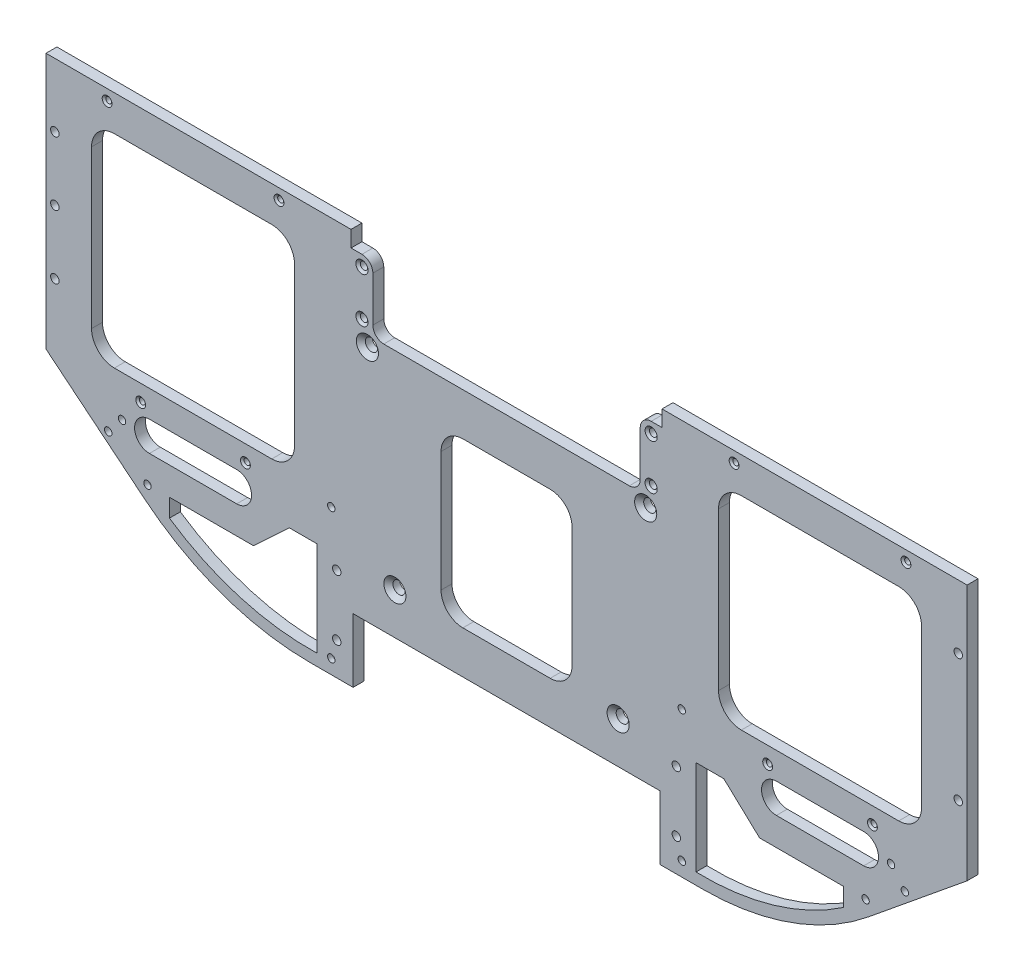
SolidWorks part; units mm, degrees
material "Acrylic (Medium-high impact)"
ref_plane "Front Plane" through (0, 0, 0) normal (0, 0, 1) x (1, 0, 0)
ref_plane "Top Plane" through (0, 0, 0) normal (0, 1, 0) x (1, 0, 0)
ref_plane "Right Plane" through (0, 0, 0) normal (1, 0, 0) x (0, 0, -1)
sketch "Sketch1" plane through (0, 0, 0) normal (0, 0, 1) x (1, 0, 0)
  line L0 (-85.5662, -233.3625) -> (-68.1037, -233.3625) construction
  line L1 (131.2863, 23.8125) -> (131.2863, -87.3125) construction
  line L2 (85.5663, 23.8125) -> (131.2863, 23.8125) construction
  line L3 (85.5663, -144.4625) -> (85.5663, 23.8125) construction
  line L6 (-79.2163, -3.175) -> (79.2162, -3.175) construction
  line L7 (-296.7037, -233.3625) -> (-68.1037, -233.3625)
  line L8 (131.2863, 23.8125) -> (131.2863, -87.3125)
  line L9 (85.5663, 23.8125) -> (131.2863, 23.8125)
  line L10 (85.5663, -3.175) -> (85.5663, 23.8125)
  line L11 (-131.6037, 20.5105) -> (-233.2037, 20.5105)
  line L12 (-131.6037, -3.175) -> (-131.6037, 20.5105)
  line L13 (-131.6037, -3.175) -> (85.5663, -3.175)
  line L14 (95.0913, -144.4625) -> (28.2786, -199.0142)
  line L15 (-182.4037, -196.215) -> (-182.4037, -51.435) construction
  line L16 (-93.5037, -196.215) -> (-271.3037, -196.215) construction
  line L17 (-268.1287, -51.435) -> (-96.6787, -51.435) construction
  line L18 (-459.8987, -144.4625) -> (-393.0861, -199.0142)
  line L19 (-233.2037, -3.175) -> (-450.3737, -3.175)
  line L20 (-233.2037, -3.175) -> (-233.2037, 20.5105)
  line L21 (-450.3737, -3.175) -> (-450.3737, -20.955)
  line L22 (-450.3737, -20.955) -> (-496.0937, -20.955)
  line L23 (-496.0937, -20.955) -> (-496.0937, -87.3125)
  line L24 (-496.0937, -20.955) -> (-450.3737, -20.955) construction
  line L25 (-450.3737, -20.955) -> (-450.3737, -144.4625) construction
  line L26 (-496.0937, -87.3125) -> (-496.0937, -20.955) construction
  arc A0 (-68.1037, -233.3625) -> (28.2786, -199.0142) centre (-68.1037, -80.9625) ccw construction
  arc A1 (95.0913, -144.4625) -> (131.2863, -87.3125) centre (-12.3507, -36.3792) ccw construction
  arc A2 (-68.1037, -233.3625) -> (28.2786, -199.0142) centre (-68.1037, -80.9625) ccw
  arc A3 (95.0913, -144.4625) -> (131.2863, -87.3125) centre (-12.3507, -36.3792) ccw
  arc A4 (-459.8987, -144.4625) -> (-496.0937, -87.3125) centre (-352.4568, -36.3792) cw
  arc A5 (-296.7037, -233.3625) -> (-393.0861, -199.0142) centre (-296.7037, -80.9625) cw
  point P39 (-182.4037, 20.5105)
  point P41 (-182.4037, -233.3625)
extrude "Boss-Extrude1" add sketch "Sketch1" along normal blind 6.35
sketch "Sketch2" plane through (0, 0, 6.35) normal (0, 0, 1) x (1, 0, 0)
  line L0 (-339.4075, -166.116) -> (-390.2075, -166.116) construction
  line L4 (-423.8625, -37.0786) -> (-423.8625, -128.6564)
  line L5 (-319.0186, -23.8125) -> (-410.5964, -23.8125)
  line L6 (-305.7525, -128.6564) -> (-305.7525, -37.0786)
  line L7 (-410.5964, -141.9225) -> (-319.0186, -141.9225)
  line L8 (-423.8625, -37.0786) -> (-423.8625, -128.6564)
  line L9 (-319.0186, -23.8125) -> (-410.5964, -23.8125)
  line L10 (-305.7525, -128.6564) -> (-305.7525, -37.0786)
  line L11 (-410.5964, -141.9225) -> (-319.0186, -141.9225)
  line L13 (-292.6397, -178.6479) -> (-292.6397, -214.3) construction
  line L14 (-292.6397, -171.5333) -> (-292.6397, -226.6383)
  line L15 (-326.4504, -188.0036) -> (-308.8, -171.5333) construction
  line L16 (-365.5822, -190.9762) -> (-335.4294, -190.9762) construction
  line L17 (-329.6361, -190.9762) -> (-308.8, -171.5333)
  line L18 (-378.5543, -190.9762) -> (-329.6361, -190.9762)
  line L19 (-308.8, -171.5333) -> (-292.6397, -171.5333)
  line L20 (-378.5543, -201.538) -> (-378.5543, -190.9762)
  line L21 (-339.4075, -174.752) -> (-390.2075, -174.752)
  line L24 (-339.4075, -157.48) -> (-390.2075, -157.48)
  line L25 (-182.4037, 20.5105) -> (-182.4037, -233.3625) construction
  line L26 (-131.6037, 20.5105) -> (-233.2037, 20.5105) construction
  line L29 (-296.7037, -233.3625) -> (-68.1037, -233.3625) construction
  line L30 (-25.4, -166.116) -> (25.4, -166.116) construction
  line L31 (-25.4, -174.752) -> (25.4, -174.752)
  line L32 (-25.4, -157.48) -> (25.4, -157.48)
  line L33 (13.7468, -201.538) -> (13.7468, -190.9762)
  line L34 (-56.0075, -171.5333) -> (-72.1678, -171.5333)
  line L35 (13.7468, -190.9762) -> (-35.1714, -190.9762)
  line L36 (-35.1714, -190.9762) -> (-56.0075, -171.5333)
  line L37 (-72.1678, -171.5333) -> (-72.1678, -226.6383)
  line L38 (45.7889, -141.9225) -> (-45.7889, -141.9225)
  line L39 (-59.055, -128.6564) -> (-59.055, -37.0786)
  line L40 (-45.7889, -23.8125) -> (45.7889, -23.8125)
  line L41 (59.055, -37.0786) -> (59.055, -128.6564)
  arc A4 (-423.8625, -128.6564) -> (-410.5964, -141.9225) centre (-410.5964, -128.6564) ccw
  arc A5 (-410.5964, -23.8125) -> (-423.8625, -37.0786) centre (-410.5964, -37.0786) ccw
  arc A6 (-305.7525, -37.0786) -> (-319.0186, -23.8125) centre (-319.0186, -37.0786) ccw
  arc A7 (-319.0186, -141.9225) -> (-305.7525, -128.6564) centre (-319.0186, -128.6564) ccw
  arc A8 (-423.8625, -128.6564) -> (-410.5964, -141.9225) centre (-410.5964, -128.6564) ccw
  arc A9 (-410.5964, -23.8125) -> (-423.8625, -37.0786) centre (-410.5964, -37.0786) ccw
  arc A10 (-305.7525, -37.0786) -> (-319.0186, -23.8125) centre (-319.0186, -37.0786) ccw
  arc A11 (-319.0186, -141.9225) -> (-305.7525, -128.6564) centre (-319.0186, -128.6564) ccw
  arc A13 (-339.4075, -174.752) -> (-339.4075, -157.48) centre (-339.4075, -166.116) ccw
  arc A15 (-377.1442, -202.4833) -> (-336.1163, -221.2644) centre (-296.7037, -80.9625) ccw construction
  arc A17 (-378.5543, -201.538) -> (-292.6397, -226.6383) centre (-296.7037, -80.9625) ccw
  arc A19 (-390.2075, -157.48) -> (-390.2075, -174.752) centre (-390.2075, -166.116) ccw
  arc A20 (-25.4, -174.752) -> (-25.4, -157.48) centre (-25.4, -166.116) cw
  arc A21 (25.4, -157.48) -> (25.4, -174.752) centre (25.4, -166.116) cw
  arc A22 (13.7468, -201.538) -> (-72.1678, -226.6383) centre (-68.1038, -80.9625) cw
  arc A23 (-45.7889, -141.9225) -> (-59.055, -128.6564) centre (-45.7889, -128.6564) cw
  arc A24 (-59.055, -37.0786) -> (-45.7889, -23.8125) centre (-45.7889, -37.0786) cw
  arc A25 (45.7889, -23.8125) -> (59.055, -37.0786) centre (45.7889, -37.0786) cw
  arc A26 (59.055, -128.6564) -> (45.7889, -141.9225) centre (45.7889, -128.6564) cw
  point P10 (-364.8075, -166.116)
  point P27 (0, -166.116)
  dimension "D2" = 8.636
  dimension "D3" = 50.8
  dimension "D1" = 0
extrude "Cut-Extrude1" cut sketch "Sketch2" against normal through all
hole_wizard "CSK for 1/4 Flat Head Machine Screw (100)1" positions "Sketch3" profile "Sketch4" countersink size "1/4" standard "ANSI Inch" end condition up to next
sketch "Sketch3" plane through (0, 0, 6.35) normal (0, 0, 1) x (1, 0, 0)
  point P0 (-247.3642, -172.085)
  point P3 (-263.3662, -57.785)
  point P6 (-117.4432, -172.085)
  point P9 (-101.4412, -57.785)
sketch "Sketch4" plane through (-247.3642, -172.085, 6.35) normal (1, 0, 0) x (0, -1, 0)
  line L0 (0, 0) -> (0, 6.35)
  line L1 (0, 6.35) -> (3.5712, 6.35)
  line L2 (3.5712, 6.35) -> (3.5712, 2.4063)
  line L3 (3.5712, 2.4063) -> (6.4389, 0)
  line L5 (6.4389, 0) -> (0, 0)
  line L6 (-3.5712, 2.4063) -> (-6.4389, 0) construction
  line L11 (0, -6.35) -> (0, 107.95) construction
  dimension "Thru Hole Dia." = 7.1425
  dimension "Thru Hole Depth" = 6.35
  dimension "Near C'Sink Dia." = 12.8778
  dimension "Near C'Sink Angle" = 100
hole_wizard "CSK for #4 Flat Head Machine Screw (100)1" positions "Sketch5" profile "Sketch6" countersink size "#4" standard "ANSI Inch" end condition through all
sketch "Sketch5" plane through (0, 0, 6.35) normal (0, 0, 1) x (1, 0, 0)
  point P0 (-334.3275, -151.5305)
  point P3 (-395.2875, -151.5305)
  point P6 (-314.8013, -9.525)
  point P9 (-414.8137, -9.525)
  point P12 (30.48, -151.5305)
  point P15 (-30.48, -151.5305)
  point P18 (50.0062, -9.525)
  point P21 (-50.0062, -9.525)
sketch "Sketch6" plane through (-334.3275, -151.5305, 6.35) normal (1, 0, 0) x (0, -1, 0)
  line L0 (0, 0) -> (0, 6.35)
  line L1 (0, 6.35) -> (1.7272, 6.35)
  line L2 (1.7272, 6.35) -> (1.7272, 0.9484)
  line L3 (1.7272, 0.9484) -> (2.8575, 0)
  line L5 (2.8575, 0) -> (0, 0)
  line L6 (-1.7272, 0.9484) -> (-2.8575, 0) construction
  line L11 (0, -6.35) -> (0, 107.95) construction
  dimension "Thru Hole Dia." = 3.4544
  dimension "Thru Hole Depth" = 6.35
  dimension "Near C'Sink Dia." = 5.715
  dimension "Near C'Sink Angle" = 100
sketch "Sketch7" plane through (0, 0, 6.35) normal (0, 0, 1) x (1, 0, 0)
  line L0 (-271.672, -233.3625) -> (-271.672, -196.215)
  line L1 (-271.672, -196.215) -> (-93.1354, -196.215)
  line L2 (-182.4037, -196.215) -> (-182.4037, -233.3625) construction
  line L3 (-296.7037, -233.3625) -> (-68.1037, -233.3625) construction
  line L4 (-93.5037, -196.215) -> (-271.3037, -196.215) construction
  line L5 (-93.1354, -233.3625) -> (-271.672, -233.3625)
  line L6 (-93.1354, -233.3625) -> (-93.1354, -196.215)
extrude "Cut-Extrude2" cut sketch "Sketch7" against normal up to next
hole_wizard "#6 Clearance Hole1" positions "Sketch21" profile "Sketch31" hole size "#6" standard "ANSI Inch" end condition up to next
sketch "Sketch21" plane through (-452.3171, -175.5643, 0) normal (0, 0, -1) x (-1, 0, 0)
  point P0 (-60.9984, -15.4755)
  point P3 (-167.9324, -49.5432)
  point P6 (-167.9324, 26.727)
  point P9 (-371.8944, 26.727)
  point P12 (-371.8944, -49.5432)
  point P15 (-478.8284, -15.4755)
sketch "Sketch31" plane through (-391.3187, -191.0397, 0) normal (1, 0, 0) x (0, 1, 0)
  line L0 (0, 0) -> (0, 6.35)
  line L1 (0, 6.35) -> (2.1526, 6.35)
  line L2 (2.1526, 6.35) -> (2.1526, 0)
  line L5 (2.1526, 0) -> (0, 0)
  line L11 (0, -6.35) -> (0, 107.95) construction
  dimension "Thru Hole Dia." = 4.3053
  dimension "Thru Hole Depth" = 6.35
hole_wizard "#6 Plastic Insert" positions "Sketch41" profile "Sketch51" legacy
sketch "Sketch41" plane through (-452.3171, -175.5643, 0) normal (0, 0, -1) x (-1, 0, 0)
  point P0 (-60.9984, -15.4755)
  point P3 (-167.9324, -49.5432)
  point P6 (-167.9324, 26.727)
  point P9 (-371.8944, 26.727)
  point P12 (-371.8944, -49.5432)
  point P15 (-478.8284, -15.4755)
sketch "Sketch51" plane through (-391.3187, -191.0397, 0) normal (1, 0, 0) x (0, 1, 0)
  line L0 (0, 0) -> (0, 3.81)
  line L1 (0, 3.81) -> (2.5273, 3.81)
  line L2 (2.5273, 3.81) -> (2.6543, 0)
  line L3 (2.6543, 0) -> (0, 0)
  line L4 (0, 110) -> (0, -10) construction
  dimension "Minor Diameter" = 5.0546
  dimension "Depth" = 3.81
  dimension "Major Diameter" = 5.3086
other "#6 Plastic Insert Hole<1>"
hole_wizard "#6 Clearance Hole2" positions "Sketch52" profile "Sketch53" hole size "#6" standard "ANSI Inch" end condition through all
sketch "Sketch52" plane through (0, 0, 0) normal (0, 0, -1) x (-1, 0, 0)
  point P0 (459.5177, -126.1745)
  point P3 (479.9012, -91.8845)
  point P6 (486.5052, -36.449)
  point P9 (-94.7103, -126.1745)
  point P12 (-121.9518, -83.6295)
  point P15 (-98.2663, 15.875)
sketch "Sketch53" plane through (-459.5177, -126.1745, 0) normal (1, 0, 0) x (0, 1, 0)
  line L0 (0, 0) -> (0, 6.35)
  line L1 (0, 6.35) -> (2.1526, 6.35)
  line L2 (2.1526, 6.35) -> (2.1526, 0)
  line L5 (2.1526, 0) -> (0, 0)
  line L11 (0, -6.35) -> (0, 107.95) construction
  dimension "Thru Hole Dia." = 4.3053
  dimension "Thru Hole Depth" = 6.35
sketch "Sketch54" plane through (0, 0, 6.35) normal (0, 0, 1) x (1, 0, 0)
  line L0 (-91.9162, -51.435) -> (-272.8912, -51.435) construction
  line L1 (-93.5037, -49.8475) -> (-271.3037, -49.8475) construction
  line L2 (-93.5037, -49.8475) -> (-93.5037, 20.5105) construction
  line L3 (-93.5037, 20.5105) -> (-271.3037, 20.5105) construction
  line L4 (-271.3037, -49.8475) -> (-271.3037, 20.5105) construction
  line L7 (-131.6037, 20.5105) -> (-233.2037, 20.5105) construction
  line L8 (-272.8912, -38.735) -> (-260.1912, -38.735)
  line L9 (-260.1912, -51.435) -> (-260.1912, -38.735)
  line L10 (-104.6162, -51.435) -> (-260.1912, -51.435)
  line L11 (-272.8912, -38.735) -> (-272.8912, 22.098)
  line L12 (-91.9162, 22.098) -> (-272.8912, 22.098)
  line L13 (-91.9162, -38.735) -> (-91.9162, 22.098)
  line L14 (-272.8912, -51.435) -> (-272.8912, 22.098) construction
  line L17 (-91.9162, -38.735) -> (-104.6162, -38.735)
  line L18 (-104.6162, -51.435) -> (-104.6162, -38.735)
  line L19 (-91.9162, -51.435) -> (-91.9162, 22.098) construction
  dimension "D1" = 1.5875
  dimension "D2" = 12.7
  dimension "D3" = 12.7
  dimension "D4" = 12.7
  dimension "D5" = 12.7
extrude "Cut-Extrude3" cut sketch "Sketch54" against normal up to next
sketch "Sketch55" plane through (0, 0, 6.35) normal (0, 0, 1) x (1, 0, 0)
  line L0 (-91.9162, -38.735) -> (-91.9162, -3.175) construction
  line L1 (-91.9162, -12.572) -> (-104.6162, -12.572)
  line L2 (-91.9162, -12.572) -> (-91.9162, -38.735)
  line L3 (-91.9162, -38.735) -> (-104.6162, -38.735)
  line L4 (-104.6162, -12.572) -> (-104.6162, -38.735)
  line L6 (-182.4037, -51.435) -> (-182.4037, -196.215) construction
  line L7 (-260.1912, -51.435) -> (-104.6162, -51.435) construction
  line L8 (-93.1354, -196.215) -> (-271.672, -196.215) construction
  line L9 (-260.1912, -12.572) -> (-260.1912, -38.735)
  line L10 (-272.8912, -38.735) -> (-260.1912, -38.735)
  line L11 (-272.8912, -12.572) -> (-272.8912, -38.735)
  line L12 (-272.8912, -12.572) -> (-260.1912, -12.572)
  line L13 (-93.5037, -9.397) -> (-134.7787, -9.397) construction
  dimension "D1" = 12.7
  dimension "D2" = 3.175
extrude "Boss-Extrude2" add sketch "Sketch55" against normal through all
fillet "Fillet3" radius 6.35 4 edges at (-104.6162, -12.572, 3.175) (-104.6162, -51.435, 3.175) (-260.1912, -51.435, 3.175) (-260.1912, -12.572, 3.175)
hole_wizard "CSK for #6 Flat Head Machine Screw (100)1" positions "Sketch56" profile "Sketch57" countersink size "#6" standard "ANSI Inch" end condition through all
sketch "Sketch56" plane through (0, 0, 6.35) normal (0, 0, 1) x (1, 0, 0)
  line L0 (-110.5963, -40.514) -> (-110.5963, -49.8475) construction
  line L2 (-95.0912, -49.8475) -> (-161.4487, -49.8475) construction
  line L3 (-101.4412, -40.514) -> (-116.6812, -40.514) construction
  line L4 (-110.5963, -45.1807) -> (-98.2662, -45.1807) construction
  point P0 (-266.5412, -18.922)
  point P8 (-98.2662, -18.922)
  point P31 (-98.2662, -45.1807)
  point P32 (-266.5412, -45.1807)
sketch "Sketch57" plane through (-266.5412, -18.922, 6.35) normal (1, 0, 0) x (0, -1, 0)
  line L0 (0, 0) -> (0, 6.35)
  line L1 (0, 6.35) -> (2.1526, 6.35)
  line L2 (2.1526, 6.35) -> (2.1526, 1.1669)
  line L3 (2.1526, 1.1669) -> (3.5433, 0)
  line L5 (3.5433, 0) -> (0, 0)
  line L6 (-2.1526, 1.1669) -> (-3.5433, 0) construction
  line L11 (0, -6.35) -> (0, 107.95) construction
  dimension "Thru Hole Dia." = 4.3053
  dimension "Thru Hole Depth" = 6.35
  dimension "Near C'Sink Dia." = 7.0866
  dimension "Near C'Sink Angle" = 100
sketch "Sketch58" plane through (0, 0, 6.35) normal (0, 0, 1) x (1, 0, 0)
  line L1 (-201.4537, -123.825) -> (-163.3537, -123.825) construction
  line L2 (-144.3037, -171.45) -> (-220.5037, -171.45)
  line L3 (-144.3037, -171.45) -> (-144.3037, -76.2)
  line L4 (-144.3037, -76.2) -> (-220.5037, -76.2)
  line L5 (-182.4037, -95.25) -> (-182.4037, -152.4) construction
  line L6 (-163.3537, -95.25) -> (-163.3537, -152.4) construction
  line L7 (-201.4537, -95.25) -> (-201.4537, -152.4) construction
  line L8 (-220.5037, -171.45) -> (-220.5037, -76.2)
  line L9 (-144.3037, -171.45) -> (-220.5037, -76.2) construction
  line L10 (-144.3037, -76.2) -> (-220.5037, -171.45) construction
  arc A0 (-163.3537, -95.25) -> (-201.4537, -95.25) centre (-182.4037, -95.25) ccw construction
  arc A1 (-201.4537, -152.4) -> (-163.3537, -152.4) centre (-182.4037, -152.4) ccw construction
  point P0 (-182.4037, -123.825)
  point P9 (-182.4037, -123.825)
  dimension "D1" = 57.15
  dimension "D2" = 38.1
  dimension "D3" = 76.2
extrude "Cut-Extrude4" cut sketch "Sketch58" against normal through all
sketch "Sketch60" plane through (0, 0, 6.35) normal (0, 0, 1) x (1, 0, 0)
  line L0 (85.5663, 23.8125) -> (85.5663, -152.2395)
  line L1 (28.2786, -199.0142) -> (95.0913, -144.4625) construction
  line L2 (131.2863, 23.8125) -> (85.5663, 23.8125) construction
  line L3 (131.2863, -87.3125) -> (131.2863, 23.8125) construction
  line L4 (131.2863, 23.8125) -> (85.5663, 23.8125)
  line L5 (131.2863, -87.3125) -> (131.2863, 23.8125)
  line L6 (85.5663, -152.2395) -> (95.0913, -144.4625)
  line L7 (-450.3737, -20.955) -> (-496.0937, -20.955) construction
  line L8 (-496.0937, -20.955) -> (-496.0937, -87.3125) construction
  line L9 (-459.8987, -144.4625) -> (-393.0861, -199.0142) construction
  line L10 (-450.3737, -20.955) -> (-496.0937, -20.955)
  line L11 (-496.0937, -20.955) -> (-496.0937, -87.3125)
  line L12 (-459.8987, -144.4625) -> (-450.3737, -152.2395)
  line L13 (-450.3737, -20.955) -> (-450.3737, -152.2395)
  arc A0 (95.0913, -144.4625) -> (131.2863, -87.3125) centre (-12.3507, -36.3792) ccw construction
  arc A1 (95.0913, -144.4625) -> (131.2863, -87.3125) centre (-12.3507, -36.3792) ccw
  arc A2 (-496.0937, -87.3125) -> (-459.8987, -144.4625) centre (-352.4568, -36.3792) ccw construction
  arc A3 (-496.0937, -87.3125) -> (-459.8987, -144.4625) centre (-352.4568, -36.3792) ccw
extrude "Cut-Extrude5" cut sketch "Sketch60" against normal through all
hole_wizard "CSK for #8 Flat Head Machine Screw (100)2" positions "Sketch61" profile "Sketch62" countersink size "#8" standard "ANSI Inch" end condition up to next
sketch "Sketch61" plane through (0, 0, 0) normal (0, 0, -1) x (-1, 0, 0)
  line L0 (281.197, -160.0558) -> (281.197, -233.3625) construction
  line L1 (296.7037, -233.3625) -> (271.672, -233.3625) construction
  line L5 (271.672, -186.69) -> (182.4037, -186.69) construction
  line L6 (182.4037, -186.69) -> (93.1355, -186.69) construction
  line L9 (445.2302, -3.175) -> (445.2302, -77.2147) construction
  line L10 (445.2302, -77.2147) -> (445.2302, -151.2545) construction
  line L11 (182.4037, -196.215) -> (182.4037, -51.435) construction
  line L12 (271.672, -196.215) -> (93.1354, -196.215) construction
  line L13 (110.9662, -51.435) -> (253.8412, -51.435) construction
  line L15 (-80.4228, -77.2147) -> (-80.4228, -151.2545) construction
  line L16 (-80.4228, -3.175) -> (-80.4228, -77.2147) construction
  line L17 (93.1355, -186.69) -> (182.4037, -186.69) construction
  line L18 (83.6104, -160.0558) -> (83.6104, -233.3625) construction
  point P0 (281.197, -214.3125)
  point P2 (281.197, -179.1058)
  point P36 (445.2302, -77.2147)
  point P41 (445.2302, -40.1949)
  point P45 (445.2302, -114.2346)
  point P61 (-80.4228, -114.2346)
  point P62 (-80.4228, -40.1949)
  point P64 (83.6104, -179.1058)
  point P65 (83.6104, -214.3125)
  dimension "D1" = 19.05
  dimension "D2" = 19.05
sketch "Sketch62" plane through (-281.197, -214.3125, 0) normal (1, 0, 0) x (0, 1, 0)
  line L0 (0, 0) -> (0, 6.35)
  line L1 (0, 6.35) -> (2.4574, 6.35)
  line L2 (2.4574, 6.35) -> (2.4574, 1.4759)
  line L3 (2.4574, 1.4759) -> (4.2164, 0)
  line L5 (4.2164, 0) -> (0, 0)
  line L6 (-2.4574, 1.4759) -> (-4.2164, 0) construction
  line L11 (0, -6.35) -> (0, 107.95) construction
  dimension "Thru Hole Dia." = 4.9149
  dimension "Thru Hole Depth" = 6.35
  dimension "Near C'Sink Dia." = 8.4328
  dimension "Near C'Sink Angle" = 100
fillet "Fillet4" radius 12.7 4 edges at (-144.3037, -171.45, 3.175) (-144.3037, -76.2, 3.175) (-220.5037, -76.2, 3.175) (-220.5037, -171.45, 3.175)
hole_wizard "CSK for #6 Flat Head Machine Screw (100)2" positions "Sketch63" profile "Sketch64" countersink size "#6" standard "ANSI Inch" end condition up to next
sketch "Sketch63" plane through (0, 0, 0) normal (0, 0, -1) x (-1, 0, 0)
  circle A0 centre (406.1283, -165.8215) radius 2.1527 construction
  circle A1 centre (414.1604, -175.659) radius 2.1526 construction
  circle A2 centre (-41.3183, -165.8233) radius 2.1527 construction
  circle A3 centre (-49.3504, -175.6607) radius 2.1526 construction
  point P0 (414.1604, -175.659)
  point P2 (406.1283, -165.8215)
  point P10 (-41.3183, -165.8233)
  point P12 (-49.3504, -175.6607)
sketch "Sketch64" plane through (-414.1604, -175.659, 0) normal (1, 0, 0) x (0, 1, 0)
  line L0 (0, 0) -> (0, 6.35)
  line L1 (0, 6.35) -> (2.1526, 6.35)
  line L2 (2.1526, 6.35) -> (2.1526, 1.1669)
  line L3 (2.1526, 1.1669) -> (3.5433, 0)
  line L5 (3.5433, 0) -> (0, 0)
  line L6 (-2.1526, 1.1669) -> (-3.5433, 0) construction
  line L11 (0, -6.35) -> (0, 107.95) construction
  dimension "Thru Hole Dia." = 4.3053
  dimension "Thru Hole Depth" = 6.35
  dimension "Near C'Sink Dia." = 7.0866
  dimension "Near C'Sink Angle" = 100
